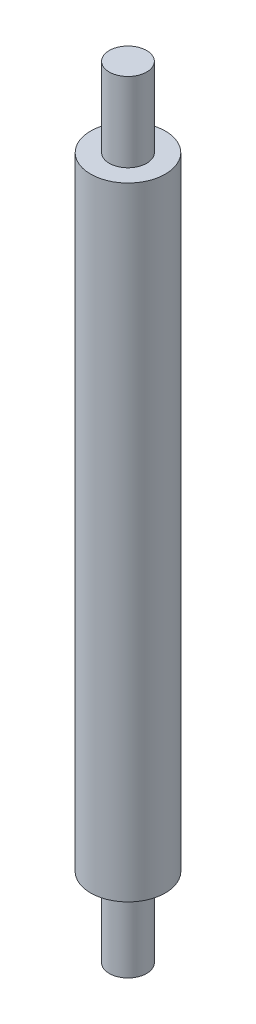
SolidWorks part; units mm, degrees
ref_plane "Front Plane" through (0, 0, 0) normal (0, 0, 1) x (1, 0, 0)
ref_plane "Top Plane" through (0, 0, 0) normal (0, 1, 0) x (1, 0, 0)
ref_plane "Right Plane" through (0, 0, 0) normal (1, 0, 0) x (0, 0, -1)
sketch "Sketch1" plane through (0, 0, 0) normal (0, 1, 0) x (1, 0, 0)
  circle A0 centre (0, 0) radius 1.5
extrude "Boss-Extrude1" add sketch "Sketch1" along normal blind 6.35
sketch "Sketch2" plane through (0, 6.35, 0) normal (0, 1, 0) x (1, 0, 0)
  circle A0 centre (0, 0) radius 3
extrude "Boss-Extrude2" add sketch "Sketch2" along normal blind 50
sketch "Sketch3" plane through (0, 56.35, 0) normal (0, 1, 0) x (1, 0, 0)
  circle A0 centre (0, 0) radius 1.5
extrude "Boss-Extrude3" add sketch "Sketch3" along normal blind 6.35
